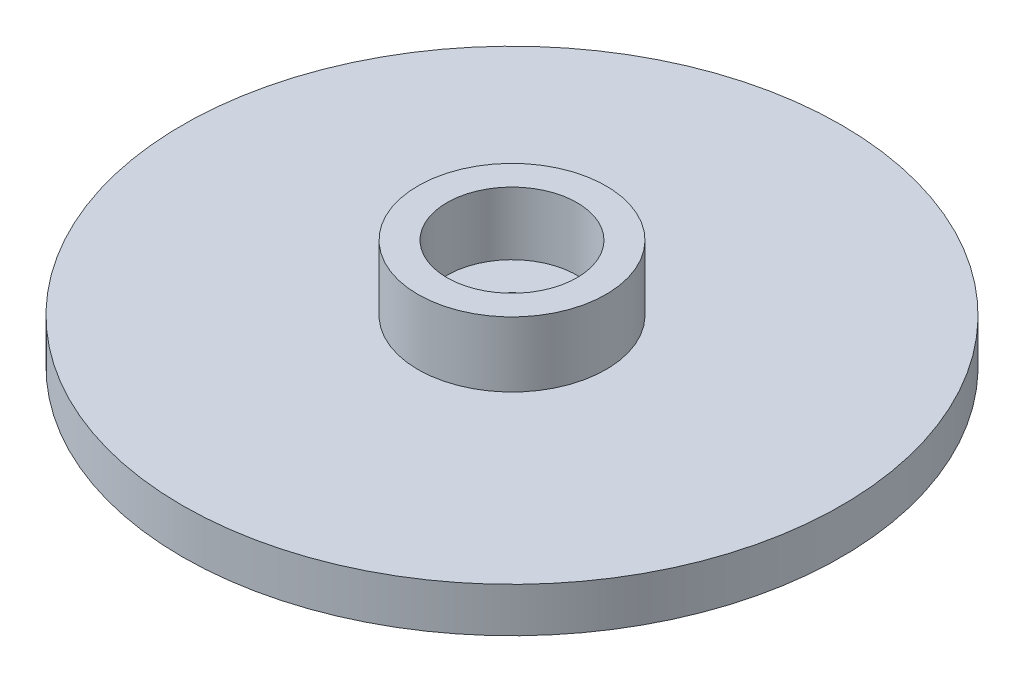
SolidWorks part; units mm, degrees
material "Nylon 101"
ref_plane "Front Plane" through (0, 0, 0) normal (0, 0, 1) x (1, 0, 0)
ref_plane "Top Plane" through (0, 0, 0) normal (0, 1, 0) x (1, 0, 0)
ref_plane "Right Plane" through (0, 0, 0) normal (1, 0, 0) x (0, 0, -1)
sketch "Sketch1" plane through (0, 0, 0) normal (0, 0, 1) x (1, 0, 0)
  line L0 (0, 0) -> (11.8364, 0)
  line L1 (11.8364, 0) -> (11.8364, 1.6002)
  line L2 (11.8364, 1.6002) -> (3.3782, 1.6002)
  line L3 (3.3782, 1.6002) -> (3.3782, 3.937)
  line L4 (3.3782, 3.937) -> (2.3368, 3.937)
  line L5 (2.3368, 3.937) -> (2.3368, 1.6764)
  line L6 (2.3368, 1.6764) -> (0, 1.6764)
  line L7 (0, 1.6764) -> (0, 0)
  line L8 (0.889, 1.6764) -> (0.889, 0)
  dimension "D1" = 2.2606
  dimension "D2" = 1.6002
  dimension "D3" = 3.937
  dimension "D4" = 11.8364
  dimension "D5" = 3.3782
  dimension "D6" = 1.0414
  dimension "D7" = 0.889
revolve "Revolve1" add sketch "Sketch1" angle 360 about L7
